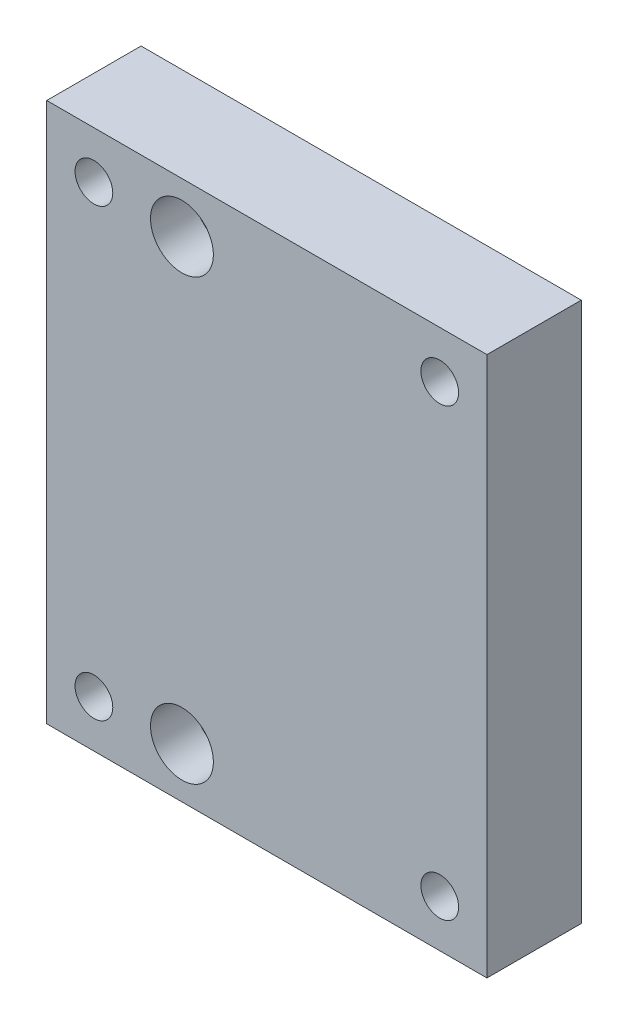
SolidWorks part; units mm, degrees
ref_plane "Płaszczyzna przednia" through (0, 0, 0) normal (0, 0, 1) x (1, 0, 0)
ref_plane "Płaszczyzna górna" through (0, 0, 0) normal (0, 1, 0) x (1, 0, 0)
ref_plane "Płaszczyzna prawa" through (0, 0, 0) normal (1, 0, 0) x (0, 0, -1)
sketch "Szkic1" plane through (0, 0, 0) normal (0, 0, 1) x (1, 0, 0)
  line L1 (35, -42.925) -> (-35, -42.925)
  line L2 (35, -42.925) -> (35, 42.925)
  line L3 (35, 42.925) -> (-35, 42.925)
  line L4 (-35, -42.925) -> (-35, 42.925)
  line L5 (35, -42.925) -> (-35, 42.925) construction
  line L6 (35, 42.925) -> (-35, -42.925) construction
  point P0 (0, 0)
  dimension "D1" = 70
  dimension "D2" = 85.85
extrude "Dodanie-wyciągnięcie1" add sketch "Szkic1" along normal blind 15
sketch "Szkic2" plane through (0, 0, 15) normal (0, 0, 1) x (1, 0, 0)
  line L0 (35, 42.925) -> (-35, 42.925) construction
  line L1 (-35, -42.925) -> (35, -42.925) construction
  line L3 (-35, 42.925) -> (-35, -42.925) construction
  circle A0 centre (-13.5, 34.925) radius 3
  circle A1 centre (-13.5, -34.925) radius 3
  dimension "D1" = 8
  dimension "D2" = 8
  dimension "D3" = 6
  dimension "D4" = 6
  dimension "D6" = 21.5
extrude "Wytnij-wyciągnięcie1" cut sketch "Szkic2" against normal blind 15
sketch "Szkic3" plane through (0, 0, 15) normal (0, 0, 1) x (1, 0, 0)
  circle A0 centre (-13.5, 34.925) radius 5
  circle A1 centre (-13.5, -34.925) radius 5
  dimension "D1" = 10
  dimension "D2" = 10
extrude "Wytnij-wyciągnięcie2" cut sketch "Szkic3" against normal blind 7
sketch "Szkic4" plane through (0, 0, 15) normal (0, 0, 1) x (1, 0, 0)
  line L0 (35, 42.925) -> (-35, 42.925) construction
  line L1 (35, -42.925) -> (35, 42.925) construction
  circle A0 centre (27.5, 35.425) radius 3
  dimension "D1" = 7.5
  dimension "D3" = 6
  dimension "D2" = 7.5
extrude "Wytnij-wyciągnięcie3" cut sketch "Szkic4" against normal blind 15
pattern_linear "Szyk liniowy1" count 2 spacing 55 along (-1, 0, 0) count 2 spacing 70.85 along (0, -1, 0) of "Wytnij-wyciągnięcie3"
